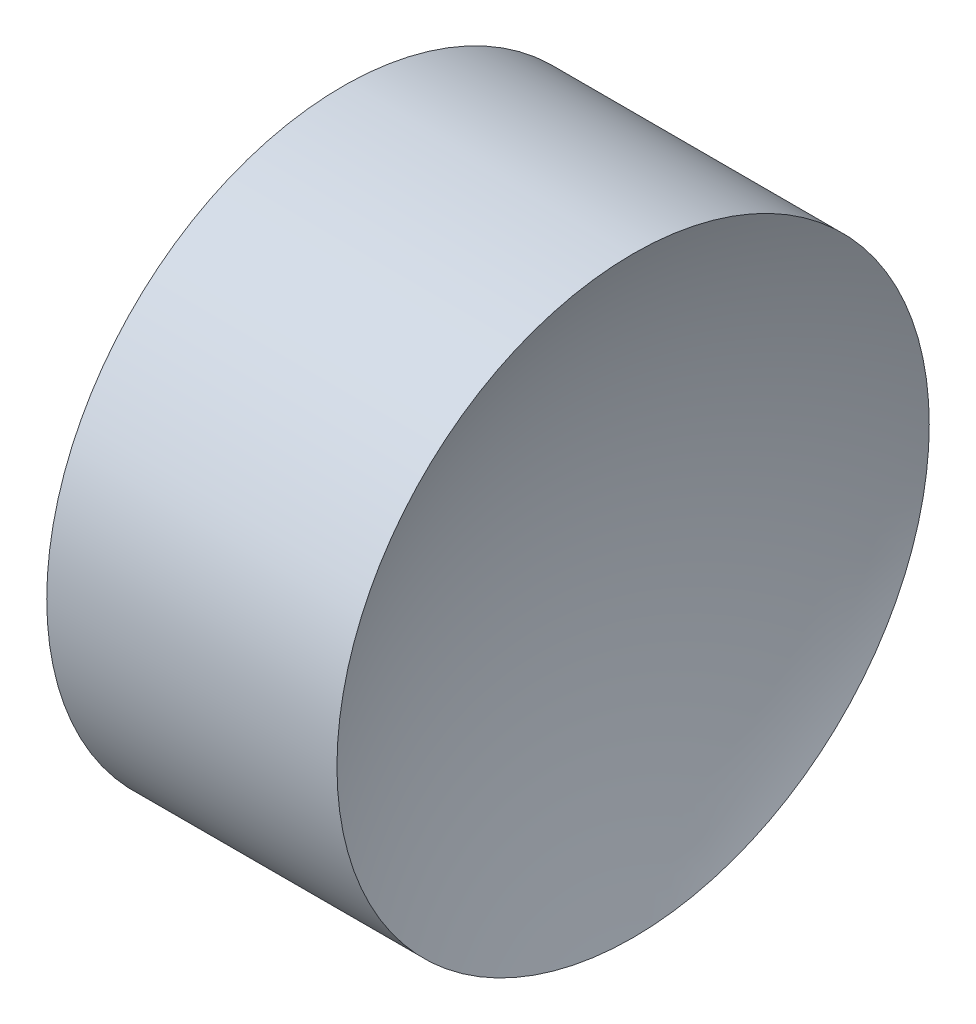
SolidWorks part; units mm, degrees
ref_plane "前视基准面" through (0, 0, 0) normal (0, 0, 1) x (1, 0, 0)
ref_plane "上视基准面" through (0, 0, 0) normal (0, 1, 0) x (1, 0, 0)
ref_plane "右视基准面" through (0, 0, 0) normal (1, 0, 0) x (0, 0, -1)
sketch "草图1" plane through (0, 0, 0) normal (0, 0, 1) x (1, 0, 0)
  line L0 (10.5782, 6.5156) -> (13.4181, 6.5156) construction
  line L1 (11.0806, 6.5156) -> (11.0806, 8.5156)
  line L2 (11.0806, 8.5156) -> (13.0404, 8.5156)
  line L3 (12.5806, 6.5156) -> (11.0806, 6.5156)
  arc A0 (13.0404, 8.5156) -> (12.5806, 6.5156) centre (17.1606, 6.5156) ccw
revolve "旋转1" add sketch "草图1" angle 360 about L0
